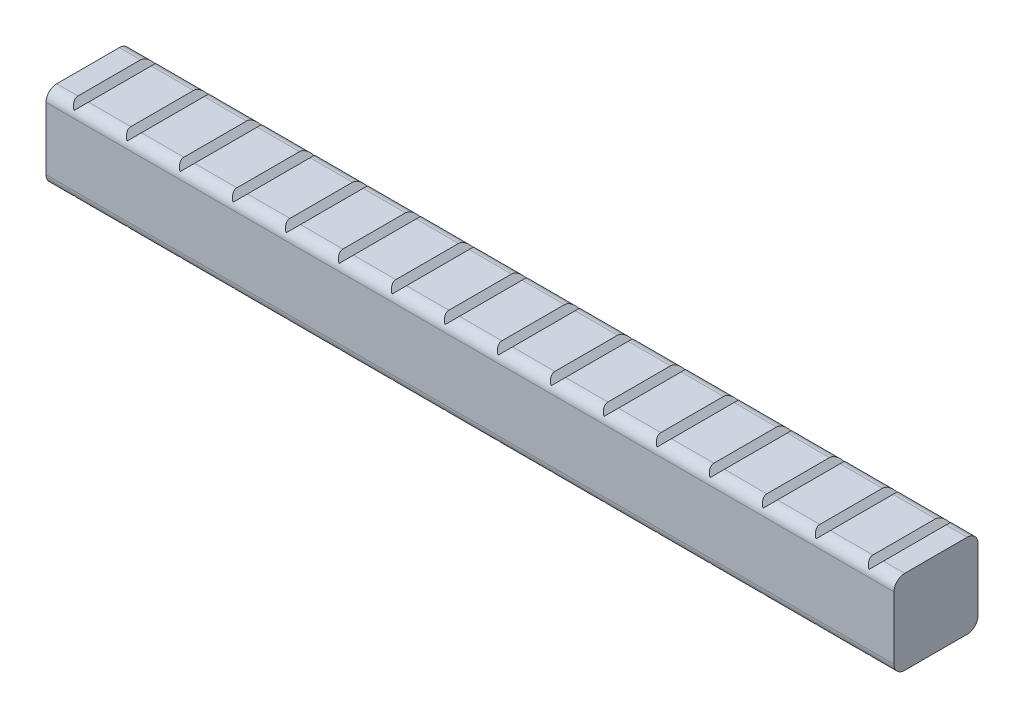
SolidWorks part; units mm, degrees
material "6061-T6 (SS)"
ref_plane "Front Plane" through (0, 0, 0) normal (0, 0, 1) x (1, 0, 0)
ref_plane "Top Plane" through (0, 0, 0) normal (0, 1, 0) x (1, 0, 0)
ref_plane "Right Plane" through (0, 0, 0) normal (1, 0, 0) x (0, 0, -1)
sketch "Sketch1" plane through (0, 0, 0) normal (1, 0, 0) x (0, 0, -1)
  line L0 (-7.5311, 10.0711) -> (-8.5832, 10.0711)
  line L1 (-7.5311, 10.0711) -> (7.5311, 10.0711)
  line L2 (-10.0711, 7.5311) -> (-10.0711, -7.5311)
  line L3 (-7.5311, -10.0711) -> (7.5311, -10.0711)
  line L4 (10.0711, 7.5311) -> (10.0711, -7.5311)
  line L5 (-10.0711, 10.0711) -> (10.0711, -10.0711) construction
  line L6 (-10.0711, -10.0711) -> (10.0711, 10.0711) construction
  line L7 (-8.5832, 10.0711) -> (-10.0711, 8.5832)
  line L8 (-10.0711, 8.5832) -> (-10.0711, 7.5311)
  line L9 (7.5311, 10.0711) -> (8.5832, 10.0711)
  line L10 (8.5832, 10.0711) -> (10.0711, 8.5832)
  line L11 (10.0711, 8.5832) -> (10.0711, 7.5311)
  line L12 (7.5311, -10.0711) -> (8.5832, -10.0711)
  line L13 (8.5832, -10.0711) -> (10.0711, -8.5832)
  line L14 (10.0711, -8.5832) -> (10.0711, -7.5311)
  line L15 (-10.0711, -7.5311) -> (-10.0711, -8.5832)
  line L16 (-10.0711, -8.5832) -> (-8.5832, -10.0711)
  line L17 (-8.5832, -10.0711) -> (-7.5311, -10.0711)
  arc A0 (-7.5311, -10.0711) -> (-10.0711, -7.5311) centre (-7.5311, -7.5311) cw construction
  arc A1 (7.5311, -10.0711) -> (10.0711, -7.5311) centre (7.5311, -7.5311) ccw construction
  arc A2 (10.0711, 7.5311) -> (7.5311, 10.0711) centre (7.5311, 7.5311) ccw construction
  arc A3 (-7.5311, 10.0711) -> (-10.0711, 7.5311) centre (-7.5311, 7.5311) ccw construction
  point P0 (0, 0)
  dimension "D2" = 2.54
  dimension "D1" = 20.1422
extrude "Boss-Extrude1" add sketch "Sketch1" along normal blind 203.2
sketch "Sketch2" plane through (0, 0, 10.0711) normal (0, 0, 1) x (1, 0, 0)
  line L0 (5.08, 10.0711) -> (6.35, 8.8011)
  line L1 (203.2, 10.0711) -> (0, 10.0711) construction
  line L2 (6.35, 8.8011) -> (7.62, 10.0711)
  line L3 (5.08, 10.0711) -> (7.62, 10.0711)
  line L4 (0, 8.5832) -> (0, -8.5832) construction
  dimension "D1" = 6.35
  dimension "D2" = 1.27
extrude "Cut-Extrude1" cut sketch "Sketch2" against normal through all
pattern_linear "LPattern1" count 16 spacing 12.7 along (1, 0, 0) of "Cut-Extrude1"
mirror "Mirror1" about plane through (0, 0, 0) normal (0, 1, 0) of "LPattern1", "Cut-Extrude1"
sketch "Sketch3" plane through (0, 0, 0) normal (-1, 0, 0) x (0, 0, 1)
  line L0 (10.0711, 8.5832) -> (10.0711, -8.5832) construction
  line L1 (8.5832, -10.0711) -> (-8.5832, -10.0711) construction
  line L2 (-10.0711, -8.5832) -> (-10.0711, 8.5832) construction
  line L3 (-8.5832, 10.0711) -> (8.5832, 10.0711) construction
  line L4 (10.0711, 8.5832) -> (10.0711, -8.5832)
  line L5 (8.5832, -10.0711) -> (-8.5832, -10.0711)
  line L6 (-10.0711, -8.5832) -> (-10.0711, 8.5832)
  line L7 (-8.5832, 10.0711) -> (8.5832, 10.0711)
  arc A0 (-10.0711, 7.5057) -> (-7.5057, 10.0711) centre (-7.5057, 7.5057) cw
  arc A1 (7.5057, 10.0711) -> (10.0711, 7.5057) centre (7.5057, 7.5057) cw
  arc A2 (10.0711, -7.5057) -> (7.5057, -10.0711) centre (7.5057, -7.5057) cw
  arc A3 (-7.5057, -10.0711) -> (-10.0711, -7.5057) centre (-7.5057, -7.5057) cw
  dimension "D1" = 2.5654
extrude "Cut-Extrude2" cut sketch "Sketch3" against normal through all flip side to cut contours A3 L5 A2 L4 A1 L7 A0 L6
